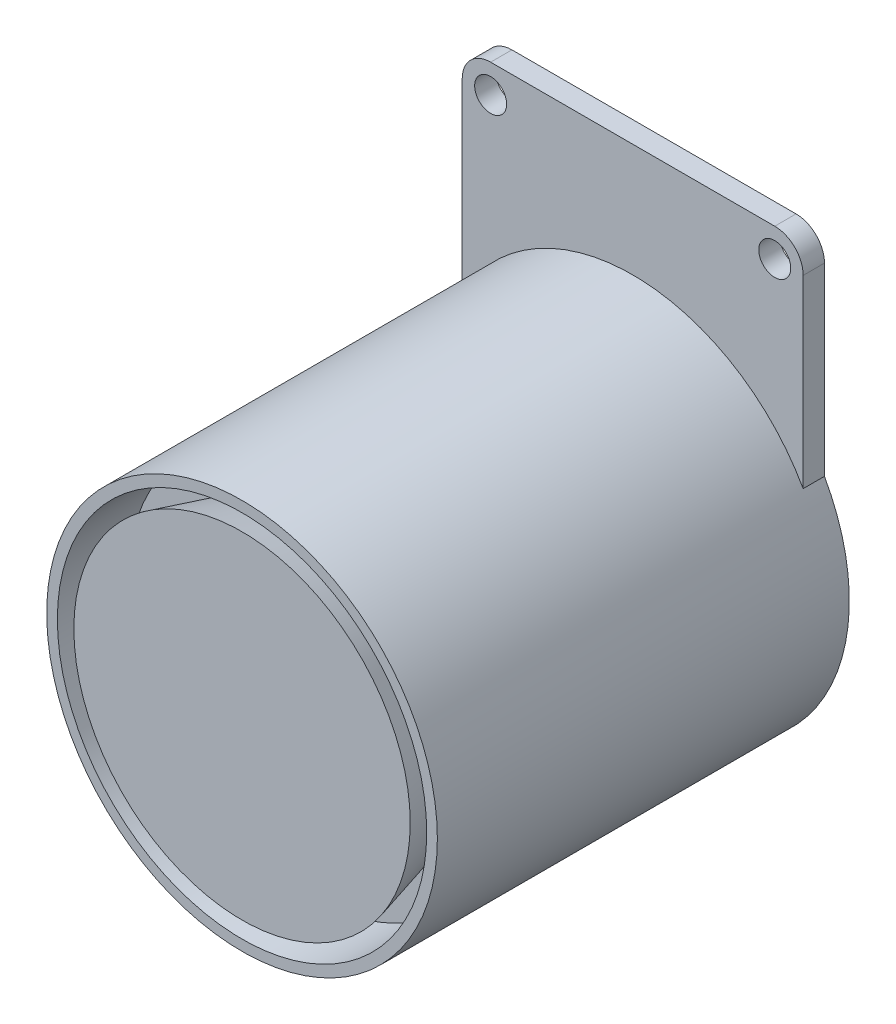
SolidWorks part; units mm, degrees
ref_plane "Płaszczyzna przednia" through (0, 0, 0) normal (0, 0, 1) x (1, 0, 0)
ref_plane "Płaszczyzna górna" through (0, 0, 0) normal (0, 1, 0) x (1, 0, 0)
ref_plane "Płaszczyzna prawa" through (0, 0, 0) normal (1, 0, 0) x (0, 0, -1)
sketch "Szkic1" plane through (0, 0, 0) normal (0, 0, 1) x (1, 0, 0)
  line L5 (-24, 13.4257) -> (24, 13.4257)
  line L6 (-24, 13.4257) -> (-24, 43.4257)
  line L7 (-24, 43.4257) -> (24, 43.4257)
  line L8 (24, 13.4257) -> (24, 43.4257)
  circle A0 centre (0, 0) radius 27.5
  dimension "D1" = 55
  dimension "D2" = 48
  dimension "D3" = 30
extrude "Dodanie-wyciągnięcie1" add sketch "Szkic1" along normal blind 3 contours L5 L8 L7 L6 | A0
sketch "Szkic2" plane through (0, 0, 3) normal (0, 0, 1) x (1, 0, 0)
  circle A0 centre (0, 0) radius 27.5
  dimension "D1" = 0
extrude "Dodanie-wyciągnięcie2" add sketch "Szkic2" along normal blind 55
sketch "Szkic3" plane through (0, 0, 58) normal (0, 0, 1) x (1, 0, 0)
  circle A0 centre (0, 0) radius 26
extrude "Wytnij-wyciągnięcie1" cut sketch "Szkic3" against normal blind 10
sketch "Szkic4" plane through (0, 0, 48) normal (0, 0, 1) x (1, 0, 0)
  circle A0 centre (0, 0) radius 21
extrude "Dodanie-wyciągnięcie3" add sketch "Szkic4" along normal blind 10 draft 15 draft outward yes
sketch "Szkic5" plane through (0, 0, 3) normal (0, 0, 1) x (1, 0, 0)
  line L0 (-24, 43.4257) -> (24, 43.4257) construction
  line L1 (-24, 13.4257) -> (-24, 43.4257) construction
  line L2 (24, 13.4257) -> (24, 43.4257) construction
  circle A0 centre (-20, 39.4257) radius 2.25
  circle A1 centre (20, 39.4257) radius 2.25
  dimension "D1" = 4
  dimension "D3" = 4.5
  dimension "D4" = 4
  dimension "D6" = 4.5
  dimension "D2" = 4
  dimension "D5" = 4
extrude "Wytnij-wyciągnięcie2" cut sketch "Szkic5" against normal up to next
fillet "Zaokrąglenie1" radius 4 2 edges at (24, 43.4257, 1.5) (-24, 43.4257, 1.5)
